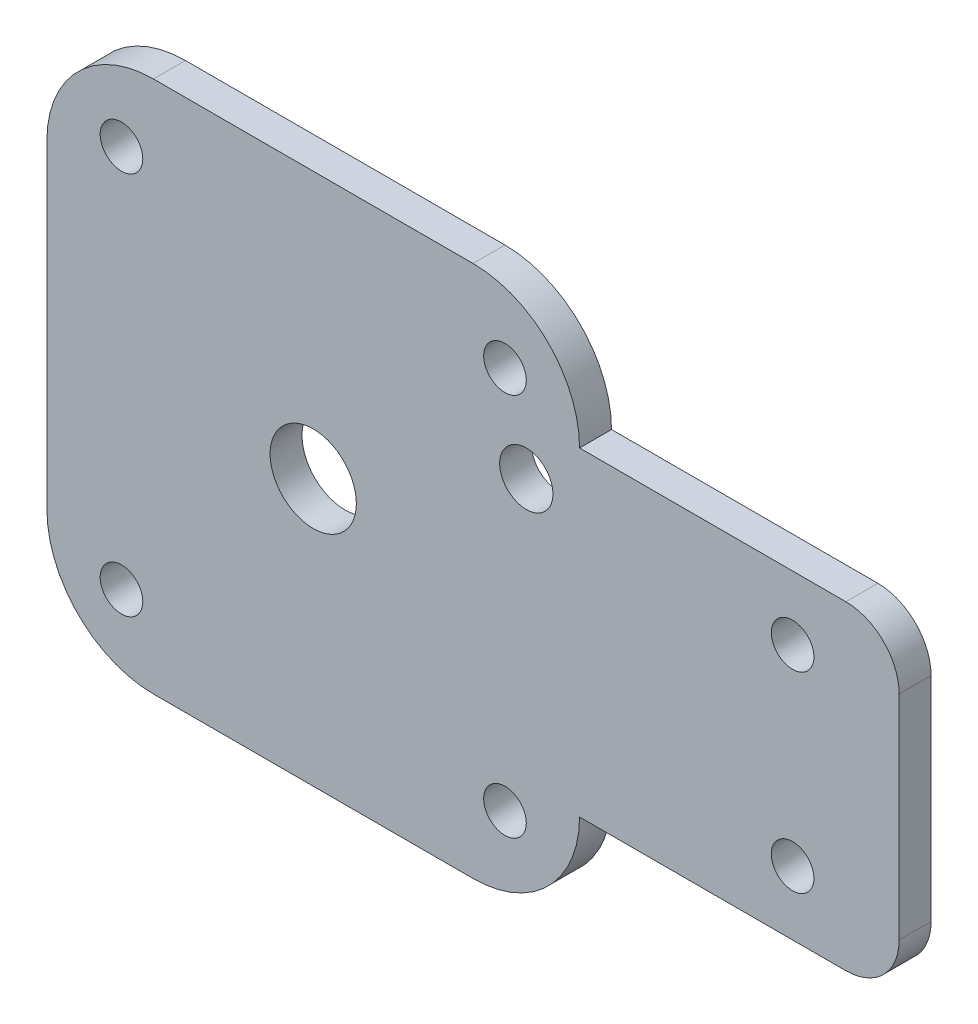
SolidWorks part; units mm, degrees
ref_plane "Alzado" through (0, 0, 0) normal (0, 0, 1) x (1, 0, 0)
ref_plane "Planta" through (0, 0, 0) normal (0, 1, 0) x (1, 0, 0)
ref_plane "Vista lateral" through (0, 0, 0) normal (1, 0, 0) x (0, 0, -1)
sketch "Croquis1" plane through (0, 0, 0) normal (0, 0, 1) x (1, 0, 0)
  line L0 (0, 25) -> (25, 25) construction
  line L1 (10, 0) -> (40, 0)
  line L2 (0, 10) -> (0, 40)
  line L3 (10, 50) -> (40, 50)
  line L4 (50, 10) -> (50, 40)
  line L5 (25, 50) -> (25, 25) construction
  line L6 (70, 34) -> (70, 16) construction
  line L7 (50, 40) -> (75, 40)
  line L8 (50, 40) -> (50, 10)
  line L9 (50, 10) -> (75, 10)
  line L10 (80, 35) -> (80, 15)
  line L11 (7, 43) -> (43, 43) construction
  line L12 (43, 7) -> (43, 43) construction
  line L13 (7, 43) -> (7, 7) construction
  line L14 (7, 7) -> (43, 7) construction
  arc A0 (10, 0) -> (0, 10) centre (10, 10) cw
  arc A1 (40, 0) -> (50, 10) centre (40, 10) ccw
  arc A2 (40, 50) -> (50, 40) centre (40, 40) cw
  arc A3 (0, 40) -> (10, 50) centre (10, 40) cw
  circle A4 centre (7, 43) radius 2
  circle A5 centre (43, 43) radius 2
  circle A6 centre (43, 7) radius 2
  circle A7 centre (7, 7) radius 2
  circle A8 centre (25, 25) radius 4.05
  arc A9 (75, 10) -> (80, 15) centre (75, 15) ccw
  arc A10 (75, 40) -> (80, 35) centre (75, 35) cw
  circle A11 centre (70, 34) radius 2
  circle A12 centre (70, 16) radius 2
  circle A13 centre (45, 35) radius 2.5
  point P7 (0, 0)
  point P12 (50, 50)
  point P15 (0, 50)
  point P34 (80, 40)
  dimension "D3" = 10
  dimension "D4" = 4
  dimension "D8" = 5
  dimension "D9" = 4
  dimension "D10" = 4
  dimension "D12" = 20
  dimension "D14" = 8.1
  dimension "D17" = 5
  dimension "D1" = 50
  dimension "D2" = 50
  dimension "D5" = 7
  dimension "D6" = 7
  dimension "D7" = 30
  dimension "D11" = 18
  dimension "D13" = 6
  dimension "D15" = 15
  dimension "D16" = 5
extrude "Saliente-Extruir1" add sketch "Croquis1" along normal blind 3 contours A3 L2 A0 L1 A1 L4 A2 L3 A13 A8 A5 A4 A6 A7 | A10 L7 L4 L9 A9 L10 A12 A11
